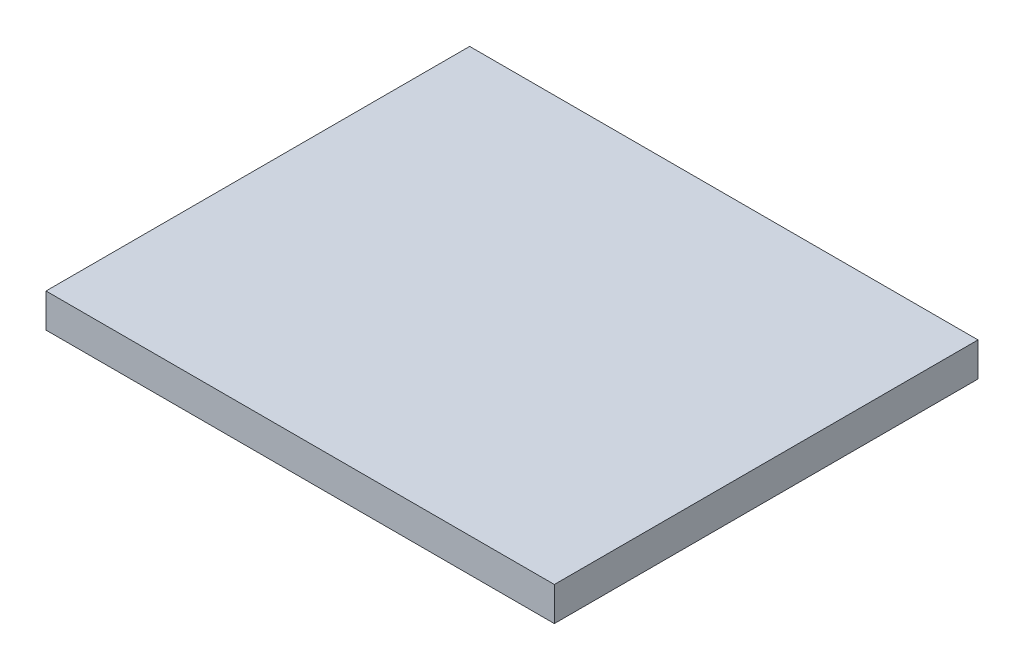
SolidWorks part; units mm, degrees
ref_plane "前视基准面" through (0, 0, 0) normal (0, 0, 1) x (1, 0, 0)
ref_plane "上视基准面" through (0, 0, 0) normal (0, 1, 0) x (1, 0, 0)
ref_plane "右视基准面" through (0, 0, 0) normal (1, 0, 0) x (0, 0, -1)
sketch "草图1" plane through (0, 0, 0) normal (1, 0, 0) x (0, 0, -1)
  line L2 (-12.5, 1) -> (12.5, 1)
  line L3 (12.5, 1) -> (12.5, -1)
  line L4 (12.5, -1) -> (-12.5, -1)
  line L5 (-12.5, 1) -> (-12.5, -1)
  dimension "D1" = 25
extrude "凸台-拉伸1" add sketch "草图1" along normal blind 30
